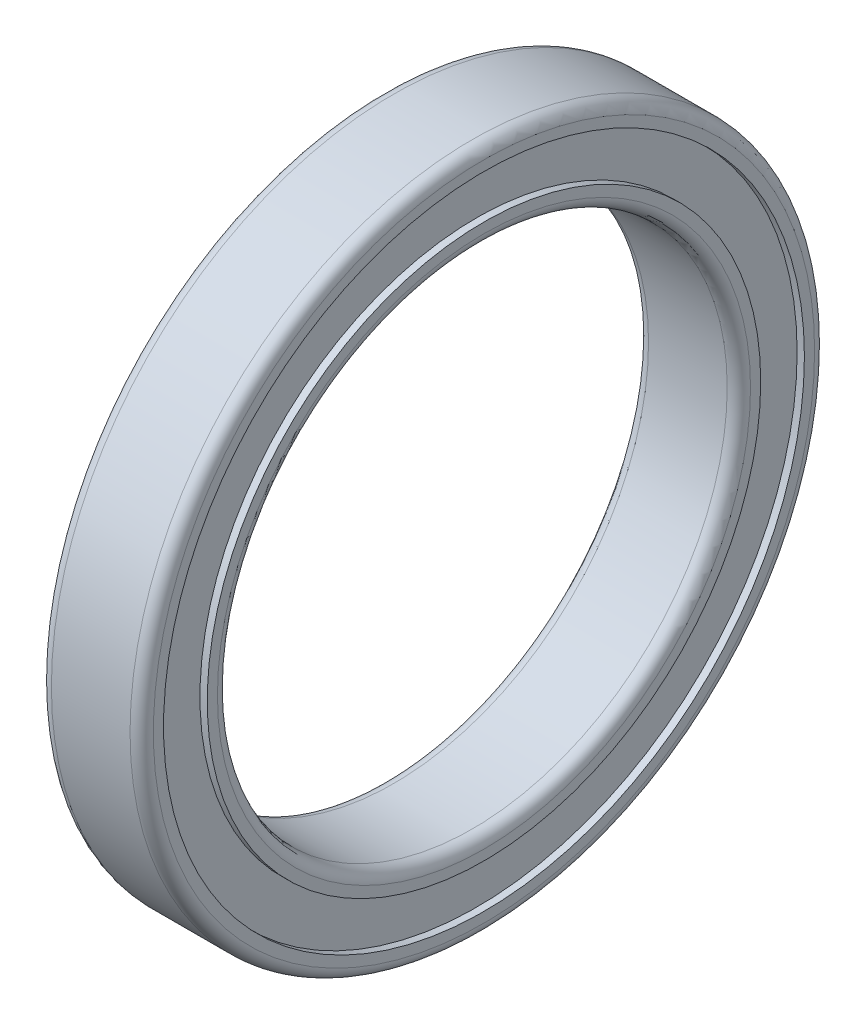
SolidWorks part; units mm, degrees
ref_plane "Спереди" through (0, 0, 0) normal (0, 0, 1) x (1, 0, 0)
ref_plane "Сверху" through (0, 0, 0) normal (0, 1, 0) x (1, 0, 0)
ref_plane "Справа" through (0, 0, 0) normal (1, 0, 0) x (0, 0, -1)
sketch "Эскиз1" plane through (0, 0, 0) normal (0, 0, 1) x (1, 0, 0)
  line L0 (0, 0) -> (-18.1184, 0) construction
  line L1 (0, 0) -> (0, 22.9845) construction
  line L2 (3.5, 17.5) -> (-3.5, 17.5)
  line L3 (-3.5, 17.5) -> (-3.5, 19)
  line L4 (-3, 19) -> (-3.5, 19)
  line L5 (-3, 19) -> (-3, 22)
  line L6 (-3, 22) -> (-3.5, 22)
  line L7 (-3.5, 22) -> (-3.5, 23.5)
  line L8 (-3.5, 23.5) -> (3.5, 23.5)
  line L9 (3.5, 22) -> (3.5, 23.5)
  line L10 (3, 22) -> (3.5, 22)
  line L11 (3, 19) -> (3, 22)
  line L12 (3, 19) -> (3.5, 19)
  line L13 (3.5, 17.5) -> (3.5, 19)
  point P13 (0, 23.5)
  point P18 (0, 17.5)
  dimension "D1" = 35
  dimension "D2" = 47
  dimension "D3" = 7
  dimension "D4" = 0.5
  dimension "D5" = 1.5
revolve "Повернуть1" add sketch "Эскиз1" angle 360 about L0
fillet "Скругление1" radius 0.8 4 edges at (3.5, 0, -23.5) (-3.5, 0, -23.5) (-3.5, 0, -17.5) (3.5, 0, -17.5)
